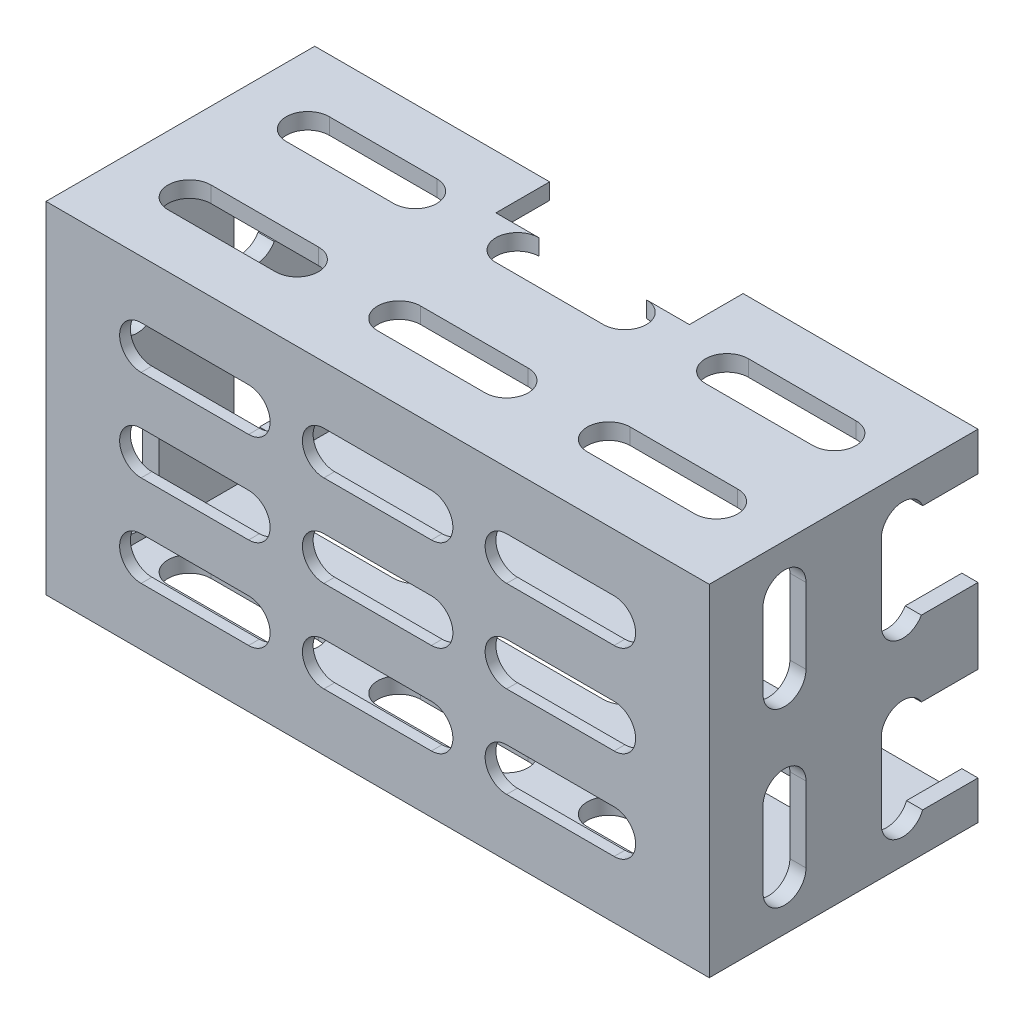
SolidWorks part; units mm, degrees
ref_plane "Front Plane" through (0, 0, 0) normal (0, 0, 1) x (1, 0, 0)
ref_plane "Top Plane" through (0, 0, 0) normal (0, 1, 0) x (1, 0, 0)
ref_plane "Right Plane" through (0, 0, 0) normal (1, 0, 0) x (0, 0, -1)
sketch "Sketch1" plane through (0, 0, 0) normal (0, 0, 1) x (1, 0, 0)
  line L4 (29.35, -14.35) -> (-29.35, -14.35)
  line L5 (29.25, -14.25) -> (-29.25, -14.25) construction
  line L6 (29.25, -14.25) -> (29.25, 14.25) construction
  line L7 (29.25, 14.25) -> (-29.25, 14.25) construction
  line L16 (-29.25, -14.25) -> (-29.25, 14.25) construction
  line L17 (-29.35, -14.35) -> (-29.35, 14.35)
  line L18 (29.35, 14.35) -> (-29.35, 14.35)
  line L19 (29.35, -14.35) -> (29.35, 14.35)
  line L20 (-30.85, -15.85) -> (-30.85, 15.85)
  line L21 (30.85, 15.85) -> (-30.85, 15.85)
  line L22 (30.85, -15.85) -> (30.85, 15.85)
  line L23 (30.85, -15.85) -> (-30.85, -15.85)
  dimension "D1" = 0.1
  dimension "D2" = 1.5
extrude "Boss-Extrude1" add sketch "Sketch1" along normal blind 19
sketch "Sketch2" plane through (0, 0, 19) normal (0, 0, 1) x (1, 0, 0)
  line L4 (-30.85, -15.85) -> (30.85, -15.85)
  line L5 (-30.85, -15.85) -> (30.85, -15.85)
  line L6 (-30.85, 15.85) -> (-30.85, -15.85)
  line L7 (30.85, 15.85) -> (-30.85, 15.85)
  line L10 (-30.85, 15.85) -> (-30.85, -15.85)
  line L11 (30.85, 15.85) -> (-30.85, 15.85)
  line L12 (30.85, -15.85) -> (30.85, 15.85)
  line L13 (30.85, -15.85) -> (30.85, 15.85)
  dimension "D1" = 0
extrude "Boss-Extrude2" add sketch "Sketch2" along normal blind 1
sketch "Sketch3" plane through (0, 0, 0) normal (0, 0, -1) x (-1, 0, 0)
  line L1 (29.35, -14.35) -> (-29.35, -14.35) construction
  line L4 (-30.85, -15.85) -> (30.85, -15.85)
  line L5 (30.85, 15.85) -> (-30.85, 15.85)
  line L6 (30.85, -15.85) -> (30.85, 15.85)
  line L7 (-30.85, -15.85) -> (30.85, -15.85)
  line L9 (30.85, 15.85) -> (9, 15.85)
  line L10 (30.85, -15.85) -> (30.85, 15.85)
  line L14 (29.35, 14.35) -> (29.35, -14.35) construction
  line L20 (-29.35, 14.35) -> (29.35, 14.35) construction
  line L21 (-29.35, -14.35) -> (-29.35, 14.35) construction
  line L22 (29.35, -14.35) -> (-29.35, -14.35)
  line L23 (29.35, 14.35) -> (29.35, -14.35)
  line L24 (-30.85, 15.85) -> (-30.85, -15.85)
  line L25 (-30.85, 15.85) -> (-30.85, -15.85)
  line L26 (-29.35, 14.35) -> (-9, 14.35)
  line L27 (-29.35, -14.35) -> (-29.35, 14.35)
  line L28 (-9, 14.35) -> (-9, 15.85)
  line L29 (9, 14.35) -> (9, 15.85)
  line L30 (-9, 15.85) -> (-30.85, 15.85)
  line L31 (9, 14.35) -> (29.35, 14.35)
  point P10 (9, 15.1)
  dimension "D2" = 18
  dimension "D1" = 0
extrude "Boss-Extrude3" add sketch "Sketch3" along normal up to surface (5 mm away)
sketch "Sketch8" plane through (0, 0, 19) normal (0, 0, -1) x (-1, 0, 0)
  line L0 (12, 6.5) -> (22, 6.5) construction
  line L1 (12, -2) -> (22, -2) construction
  line L2 (12, -10.5) -> (22, -10.5) construction
  line L3 (-5, -10.5) -> (5, -10.5) construction
  line L4 (-22, -10.5) -> (-12, -10.5) construction
  line L5 (-22, -2) -> (-12, -2) construction
  line L6 (-5, 6.5) -> (5, 6.5) construction
  line L7 (-22, 6.5) -> (-12, 6.5) construction
  line L8 (12, 6.5) -> (22, 6.5)
  line L9 (12, -2) -> (22, -2)
  line L10 (12, -10.5) -> (22, -10.5)
  line L11 (-5, -10.5) -> (5, -10.5)
  line L12 (-22, -10.5) -> (-12, -10.5)
  line L13 (-22, -2) -> (-12, -2)
  line L14 (-5, 6.5) -> (5, 6.5)
  line L15 (-22, 6.5) -> (-12, 6.5)
  line L16 (22, -6.5) -> (12, -6.5) construction
  line L17 (5, -6.5) -> (-5, -6.5) construction
  line L18 (-12, -6.5) -> (-22, -6.5) construction
  line L19 (22, 2) -> (12, 2) construction
  line L20 (-5, -2) -> (5, -2) construction
  line L21 (5, 2) -> (-5, 2) construction
  line L22 (-12, 2) -> (-22, 2) construction
  line L23 (22, 10.5) -> (12, 10.5) construction
  line L24 (5, 10.5) -> (-5, 10.5) construction
  line L25 (-12, 10.5) -> (-22, 10.5) construction
  line L26 (22, -6.5) -> (12, -6.5)
  line L27 (5, -6.5) -> (-5, -6.5)
  line L28 (-12, -6.5) -> (-22, -6.5)
  line L29 (22, 2) -> (12, 2)
  line L30 (-5, -2) -> (5, -2)
  line L31 (5, 2) -> (-5, 2)
  line L32 (-12, 2) -> (-22, 2)
  line L33 (22, 10.5) -> (12, 10.5)
  line L34 (5, 10.5) -> (-5, 10.5)
  line L35 (-12, 10.5) -> (-22, 10.5)
  arc A0 (22, -10.5) -> (22, -6.5) centre (22, -8.5) ccw construction
  arc A1 (12, -6.5) -> (12, -10.5) centre (12, -8.5) ccw construction
  arc A2 (5, -10.5) -> (5, -6.5) centre (5, -8.5) ccw construction
  arc A3 (-5, -6.5) -> (-5, -10.5) centre (-5, -8.5) ccw construction
  arc A4 (-12, -10.5) -> (-12, -6.5) centre (-12, -8.5) ccw construction
  arc A5 (-22, -6.5) -> (-22, -10.5) centre (-22, -8.5) ccw construction
  arc A6 (22, -2) -> (22, 2) centre (22, 0) ccw construction
  arc A7 (12, 2) -> (12, -2) centre (12, 0) ccw construction
  arc A8 (-5, 2) -> (-5, -2) centre (-5, 0) ccw construction
  arc A9 (5, -2) -> (5, 2) centre (5, 0) ccw construction
  arc A10 (-12, -2) -> (-12, 2) centre (-12, 0) ccw construction
  arc A11 (-22, 2) -> (-22, -2) centre (-22, 0) ccw construction
  arc A12 (22, 6.5) -> (22, 10.5) centre (22, 8.5) ccw construction
  arc A13 (12, 10.5) -> (12, 6.5) centre (12, 8.5) ccw construction
  arc A14 (-5, 10.5) -> (-5, 6.5) centre (-5, 8.5) ccw construction
  arc A15 (-12, 6.5) -> (-12, 10.5) centre (-12, 8.5) ccw construction
  arc A16 (-22, 10.5) -> (-22, 6.5) centre (-22, 8.5) ccw construction
  arc A17 (22, -10.5) -> (22, -6.5) centre (22, -8.5) ccw
  arc A18 (12, -6.5) -> (12, -10.5) centre (12, -8.5) ccw
  arc A19 (5, -10.5) -> (5, -6.5) centre (5, -8.5) ccw
  arc A20 (-5, -6.5) -> (-5, -10.5) centre (-5, -8.5) ccw
  arc A21 (-12, -10.5) -> (-12, -6.5) centre (-12, -8.5) ccw
  arc A22 (-22, -6.5) -> (-22, -10.5) centre (-22, -8.5) ccw
  arc A23 (22, -2) -> (22, 2) centre (22, 0) ccw
  arc A24 (12, 2) -> (12, -2) centre (12, 0) ccw
  arc A25 (-5, 2) -> (-5, -2) centre (-5, 0) ccw
  arc A26 (5, -2) -> (5, 2) centre (5, 0) ccw
  arc A27 (-12, -2) -> (-12, 2) centre (-12, 0) ccw
  arc A28 (-22, 2) -> (-22, -2) centre (-22, 0) ccw
  arc A29 (22, 6.5) -> (22, 10.5) centre (22, 8.5) ccw
  arc A30 (12, 10.5) -> (12, 6.5) centre (12, 8.5) ccw
  arc A31 (-5, 10.5) -> (-5, 6.5) centre (-5, 8.5) ccw
  arc A32 (-12, 6.5) -> (-12, 10.5) centre (-12, 8.5) ccw
  arc A33 (-22, 10.5) -> (-22, 6.5) centre (-22, 8.5) ccw
  arc A34 (5, 6.5) -> (5, 10.5) centre (5, 8.5) ccw construction
  arc A35 (5, 6.5) -> (5, 10.5) centre (5, 8.5) ccw
extrude "Cut-Extrude4" cut sketch "Sketch8" against normal through all
sketch "Sketch5" plane through (-15, 15.85, 0) normal (0, -1, 0) x (1, 0, 0)
  line L0 (-9.5, 2) -> (0.5, 2) construction
  line L1 (-9.5, 4) -> (0.5, 4)
  line L2 (-9.5, 0) -> (0.5, 0)
  line L3 (-15.85, 7.5) -> (45.85, 7.5) construction
  line L4 (45.85, -5) -> (-15.85, -5) construction
  line L5 (-15.85, 20) -> (45.85, 20) construction
  line L6 (15, -5) -> (15, 20) construction
  line L7 (45.85, 13) -> (-15.85, 13) construction
  line L8 (-15.85, 20) -> (-15.85, -5) construction
  line L9 (-4.5, 20) -> (-4.5, -5) construction
  line L10 (45.85, 2) -> (-15.85, 2) construction
  line L11 (34.5, 20) -> (34.5, -5) construction
  line L13 (10, 0) -> (20, 0)
  line L14 (10, 4) -> (20, 4)
  line L15 (10, 2) -> (20, 2) construction
  line L16 (29.5, 0) -> (39.5, 0)
  line L17 (29.5, 4) -> (39.5, 4)
  line L18 (29.5, 2) -> (39.5, 2) construction
  line L19 (10, 11) -> (20, 11)
  line L20 (10, 15) -> (20, 15)
  line L21 (10, 13) -> (20, 13) construction
  line L22 (29.5, 11) -> (39.5, 11)
  line L23 (29.5, 15) -> (39.5, 15)
  line L24 (29.5, 13) -> (39.5, 13) construction
  line L25 (-9.5, 11) -> (0.5, 11)
  line L26 (-9.5, 15) -> (0.5, 15)
  line L27 (-9.5, 13) -> (0.5, 13) construction
  line L28 (45.85, 20) -> (45.85, -5) construction
  arc A0 (-9.5, 4) -> (-9.5, 0) centre (-9.5, 2) ccw
  arc A1 (0.5, 0) -> (0.5, 4) centre (0.5, 2) ccw
  arc A2 (10, 4) -> (10, 0) centre (10, 2) ccw
  arc A3 (20, 0) -> (20, 4) centre (20, 2) ccw
  arc A4 (29.5, 4) -> (29.5, 0) centre (29.5, 2) ccw
  arc A5 (39.5, 0) -> (39.5, 4) centre (39.5, 2) ccw
  arc A6 (10, 15) -> (10, 11) centre (10, 13) ccw
  arc A7 (20, 11) -> (20, 15) centre (20, 13) ccw
  arc A8 (29.5, 15) -> (29.5, 11) centre (29.5, 13) ccw
  arc A9 (39.5, 11) -> (39.5, 15) centre (39.5, 13) ccw
  arc A10 (-9.5, 15) -> (-9.5, 11) centre (-9.5, 13) ccw
  arc A11 (0.5, 11) -> (0.5, 15) centre (0.5, 13) ccw
  point P2 (-4.5, 2)
  point P15 (45.85, 7.5)
  point P29 (15, -5)
  point P31 (15, 2)
  point P38 (34.5, 2)
  point P45 (15, 13)
  point P52 (34.5, 13)
  point P59 (-4.5, 13)
  dimension "D1" = 10
  dimension "D2" = 4
  dimension "D3" = 39
  dimension "D4" = 11
  dimension "D5" = 3
  dimension "D6" = 2
extrude "Cut-Extrude2" cut sketch "Sketch5" along normal through all
sketch "Sketch7" plane through (30.85, -15, 0) normal (-1, 0, 0) x (0, 0, -1)
  line L0 (-13, -26.5) -> (-13, -19.5) construction
  line L1 (-15, -26.5) -> (-15, -19.5)
  line L2 (-11, -26.5) -> (-11, -19.5)
  line L3 (-20, -15) -> (5, -15) construction
  line L4 (-20, -30.85) -> (-20, 0.85) construction
  line L5 (5, 0.85) -> (5, -30.85) construction
  line L6 (-7.5, 0.85) -> (-7.5, -30.85) construction
  line L7 (-20, 0.85) -> (5, 0.85) construction
  line L8 (-20, -30.85) -> (5, -30.85) construction
  line L9 (-13, -30.85) -> (-13, 0.85) construction
  line L10 (-20, -7) -> (5, -7) construction
  line L11 (-20, -23) -> (5, -23) construction
  line L12 (-2, -30.85) -> (-2, 0.85) construction
  line L13 (0, -26.5) -> (0, -19.5)
  line L14 (-4, -26.5) -> (-4, -19.5)
  line L15 (-2, -26.5) -> (-2, -19.5) construction
  line L16 (0, -10.5) -> (0, -3.5)
  line L17 (-4, -10.5) -> (-4, -3.5)
  line L18 (-2, -10.5) -> (-2, -3.5) construction
  line L19 (-11, -10.5) -> (-11, -3.5)
  line L20 (-15, -10.5) -> (-15, -3.5)
  line L21 (-13, -10.5) -> (-13, -3.5) construction
  arc A0 (-15, -26.5) -> (-11, -26.5) centre (-13, -26.5) ccw
  arc A1 (-11, -19.5) -> (-15, -19.5) centre (-13, -19.5) ccw
  arc A2 (-4, -26.5) -> (0, -26.5) centre (-2, -26.5) ccw
  arc A3 (0, -19.5) -> (-4, -19.5) centre (-2, -19.5) ccw
  arc A4 (-4, -10.5) -> (0, -10.5) centre (-2, -10.5) ccw
  arc A5 (0, -3.5) -> (-4, -3.5) centre (-2, -3.5) ccw
  arc A6 (-15, -10.5) -> (-11, -10.5) centre (-13, -10.5) ccw
  arc A7 (-11, -3.5) -> (-15, -3.5) centre (-13, -3.5) ccw
  point P2 (-13, -23)
  point P16 (-20, -15)
  point P32 (-2, -23)
  point P39 (-2, -7)
  point P46 (-13, -7)
  dimension "D1" = 7
  dimension "D2" = 4
  dimension "D3" = 16
  dimension "D6" = 11
  dimension "D4" = 2
  dimension "D5" = 2
extrude "Cut-Extrude3" cut sketch "Sketch7" along normal through all
sketch "Sketch9" plane through (-30.85, 0, 0) normal (-1, 0, 0) x (0, 0, 1)
  line L0 (-5, 0) -> (20, 0) construction
  line L1 (-5, 3.5) -> (2, 3.5)
  line L2 (-5, 3.5) -> (-5, 12.25)
  line L3 (-5, 12.25) -> (2, 12.25)
  line L4 (2, 3.5) -> (2, 12.25)
  line L6 (-5, -15.85) -> (-5, 15.85) construction
  line L7 (20, 15.85) -> (20, -15.85) construction
  line L8 (2, -3.5) -> (2, -12.25)
  line L9 (-5, -12.25) -> (2, -12.25)
  line L10 (-5, -3.5) -> (-5, -12.25)
  line L11 (-5, -3.5) -> (2, -3.5)
  arc A0 (4, 11.5) -> (0, 11.5) centre (2, 11.5) ccw construction
  point P22 (2, 13.5)
extrude "Cut-Extrude5" cut sketch "Sketch9" against normal through all
